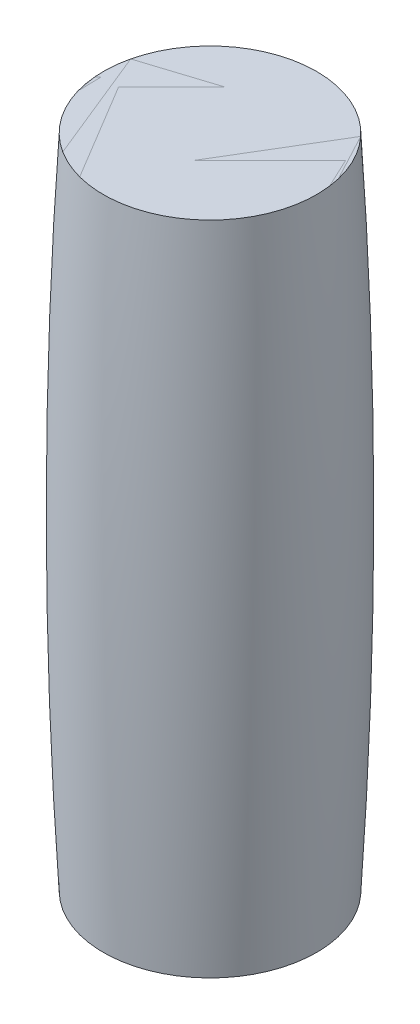
SolidWorks part; units mm, degrees
other "COLL.CYLINDER-Estrusione-Estrusione1"
ref_plane "Piano frontale" through (0, 0, 0) normal (0, 0, 1) x (1, 0, 0)
ref_plane "Piano superiore" through (0, 0, 0) normal (0, 1, 0) x (1, 0, 0)
ref_plane "Piano destro" through (0, 0, 0) normal (1, 0, 0) x (0, 0, -1)
sketch "Schizzo1" plane through (0, 0, 0) normal (0, 0, 1) x (1, 0, 0)
  line L0 (0, 0) -> (0, 66.9906) construction
  line L1 (0, 0) -> (-65, 0)
  line L2 (-65, 0) -> (-65, 400) construction
  line L3 (-65, 400) -> (0, 400)
  line L4 (0, 0) -> (0, 400)
  arc A0 (-65, 400) -> (-65, 0) centre (3528.5142, 200) ccw
  dimension "D1" = 65
  dimension "D2" = 400
revolve "Rivoluzione1" add sketch "Schizzo1" angle 360 about L4
sketch "Schizzo2" plane through (0, 0, 0) normal (0, -1, 0) x (1, 0, 0)
  circle A0 centre (0, 0) radius 65
  circle A1 centre (0, 0) radius 65 construction
extrude "Estrusione-Estrusione1" add sketch "Schizzo2" against normal up to surface (400 mm away) separate body up to face at (0, 400, -65)
